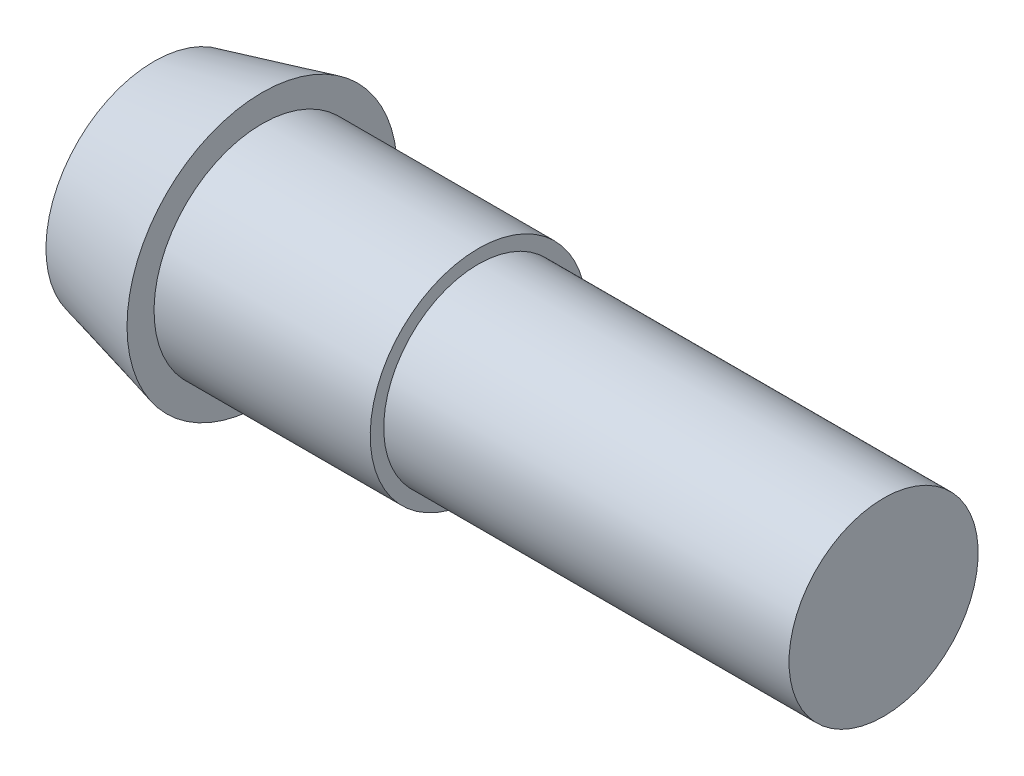
SolidWorks part; units mm, degrees
ref_plane "Спереди" through (0, 0, 0) normal (0, 0, 1) x (1, 0, 0)
ref_plane "Сверху" through (0, 0, 0) normal (0, 1, 0) x (1, 0, 0)
ref_plane "Справа" through (0, 0, 0) normal (1, 0, 0) x (0, 0, -1)
sketch "Эскиз1" plane through (0, 0, 0) normal (0, 0, 1) x (1, 0, 0)
  line L0 (0, 0) -> (0, 4)
  line L1 (0, 4) -> (4, 5)
  line L3 (4, 5) -> (4, 4)
  line L4 (4, 4) -> (12, 4)
  line L5 (12, 4) -> (12, 3.5)
  line L6 (12, 3.5) -> (27, 3.5)
  line L7 (27, 3.5) -> (27, 0)
  line L8 (27, 0) -> (0, 0)
  dimension "D1" = 4
  dimension "D2" = 8
  dimension "D3" = 4
  dimension "D4" = 1
  dimension "D5" = 5
  dimension "D6" = 27
  dimension "D7" = 0.5
revolve "Повернуть1" add sketch "Эскиз1" angle 360 about L8
